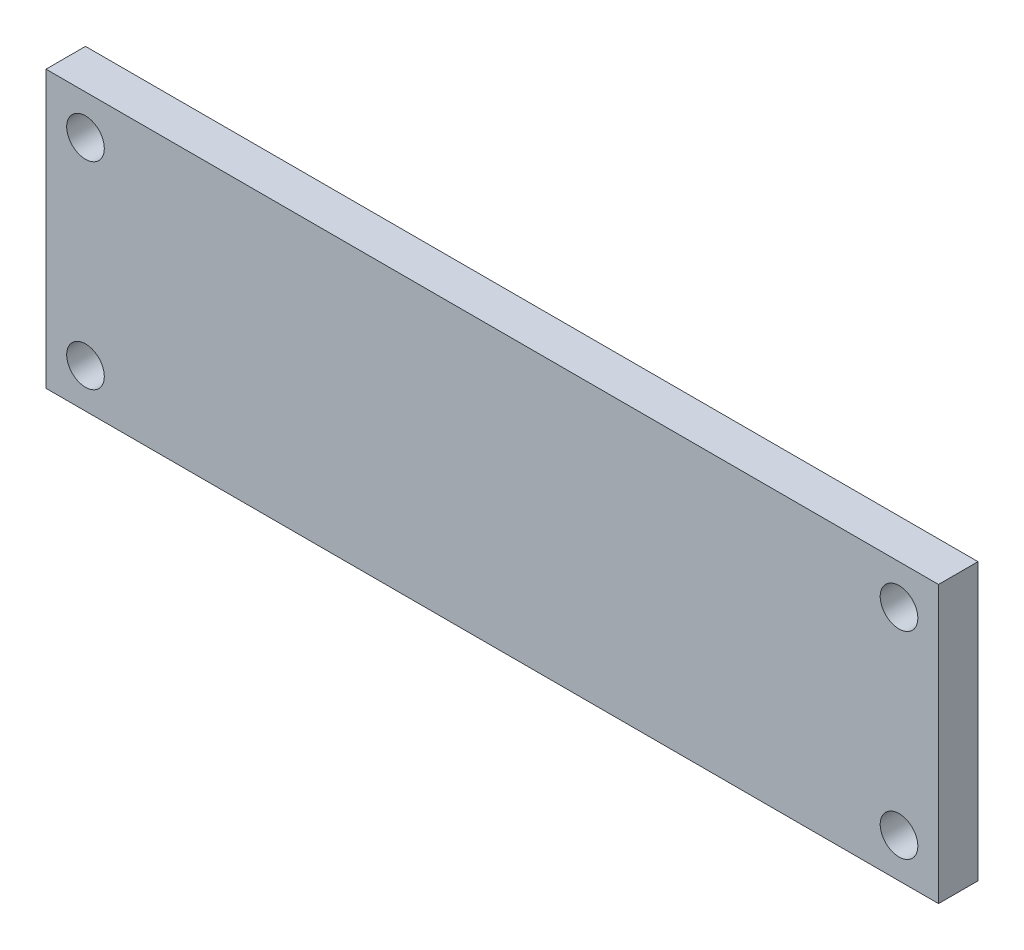
SolidWorks part; units mm, degrees
ref_plane "Front Plane" through (0, 0, 0) normal (0, 0, 1) x (1, 0, 0)
ref_plane "Top Plane" through (0, 0, 0) normal (0, 1, 0) x (1, 0, 0)
ref_plane "Right Plane" through (0, 0, 0) normal (1, 0, 0) x (0, 0, -1)
sketch "Sketch1" plane through (0, 0, 0) normal (0, 0, 1) x (1, 0, 0)
  line L1 (0, 0) -> (113, 0)
  line L2 (0, 0) -> (0, 35)
  line L3 (0, 35) -> (113, 35)
  line L4 (113, 0) -> (113, 35)
  circle A0 centre (5, 5) radius 2.3813
  circle A1 centre (5, 30) radius 2.3813
  circle A2 centre (108, 30) radius 2.3813
  circle A3 centre (108, 5) radius 2.3813
  dimension "D4" = 4.7625
  dimension "D5" = 4.7625
  dimension "D9" = 4.7625
  dimension "D11" = 4.7625
  dimension "D1" = 5
  dimension "D2" = 5
  dimension "D3" = 5
  dimension "D6" = 5
  dimension "D7" = 25
  dimension "D8" = 113
  dimension "D10" = 5
extrude "Boss-Extrude1" add sketch "Sketch1" along normal blind 5
